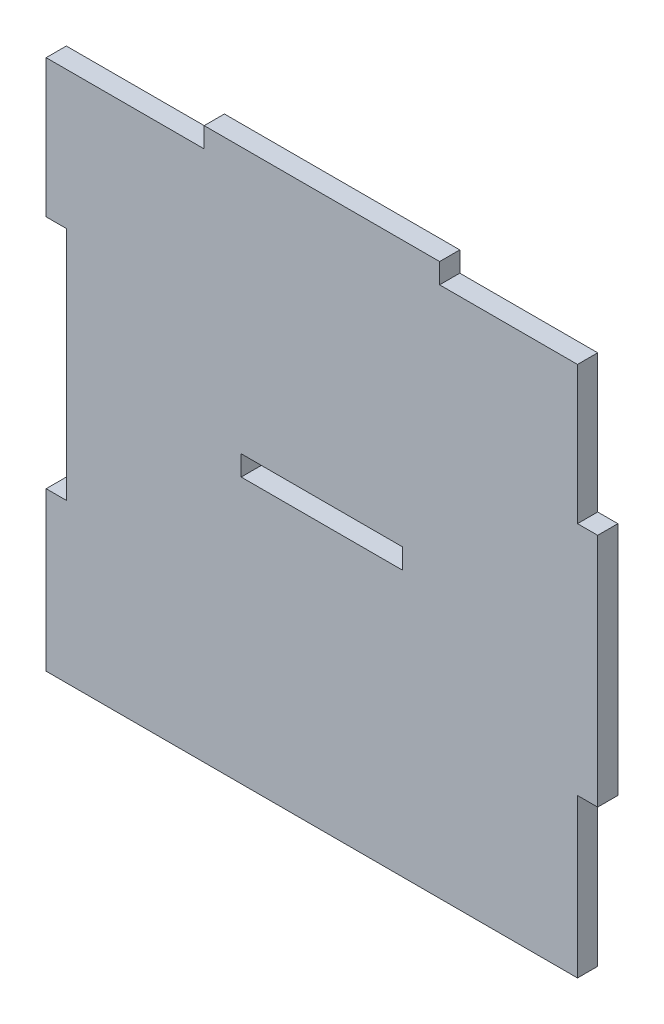
SolidWorks part; units mm, degrees
ref_plane "Front Plane" through (0, 0, 0) normal (0, 0, 1) x (1, 0, 0)
ref_plane "Top Plane" through (0, 0, 0) normal (0, 1, 0) x (1, 0, 0)
ref_plane "Right Plane" through (0, 0, 0) normal (1, 0, 0) x (0, 0, -1)
sketch "Sketch1" plane through (0, 0, 0) normal (0, 0, 1) x (1, 0, 0)
  line L0 (0, 38) -> (0, -39.5) construction
  line L5 (-38, 39.5) -> (-17.5, 39.5)
  line L6 (-38, 16) -> (-38, -16)
  line L24 (38, 39.5) -> (38, 19)
  line L26 (-41, -39.5) -> (38, -39.5)
  line L27 (-38, 0) -> (38, 0) construction
  line L28 (-17.5, 39.5) -> (-17.5, 42.5)
  line L29 (-17.5, 42.5) -> (17.5, 42.5)
  line L30 (17.5, 42.5) -> (17.5, 39.5)
  line L33 (-41, 19) -> (-41, 39.5)
  line L34 (-41, 39.5) -> (-38, 39.5)
  line L35 (-41, -19) -> (-41, -39.5)
  line L36 (38, -19) -> (38, -39.5)
  line L43 (41, 16) -> (41, -16)
  line L44 (-38, 16) -> (-38, 19)
  line L46 (17.5, 39.5) -> (38, 39.5)
  line L48 (-38, 19) -> (-41, 19)
  line L50 (-41, -19) -> (-41, -16)
  line L51 (-41, -16) -> (-38, -16)
  line L52 (38, -19) -> (38, -16)
  line L53 (38, -16) -> (41, -16)
  line L54 (41, 16) -> (41, 19)
  line L55 (41, 19) -> (38, 19)
  point P0 (0, 0)
  dimension "D1" = 79
  dimension "D2" = 76
  dimension "D3" = 3
  dimension "D4" = 35
  dimension "D5" = 3
  dimension "D6" = 76
  dimension "D7" = 35
  dimension "D8" = 3
  dimension "D9" = 3
  dimension "D10" = 3
  dimension "D11" = 3
  dimension "D12" = 35
  dimension "D13" = 0
  dimension "D14" = 20.5
extrude "Boss-Extrude1" add sketch "Sketch1" along normal blind 3
sketch "Sketch2" plane through (0, 0, 3) normal (0, 0, 1) x (1, 0, 0)
  line L0 (-41, -39.5) -> (38, -39.5) construction
  line L5 (-12, 3) -> (12, 3)
  line L6 (-12, 3) -> (-12, 0)
  line L7 (-12, 0) -> (12, 0)
  line L8 (12, 3) -> (12, 0)
  line L9 (-12, 3) -> (12, 0) construction
  line L10 (-12, 0) -> (12, 3) construction
  point P0 (0, 0)
  point P1 (0, 1.5)
  dimension "D1" = 24
  dimension "D2" = 3
  dimension "D3" = 0
  dimension "D4" = 41
extrude "Cut-Extrude1" cut sketch "Sketch2" against normal blind 3
